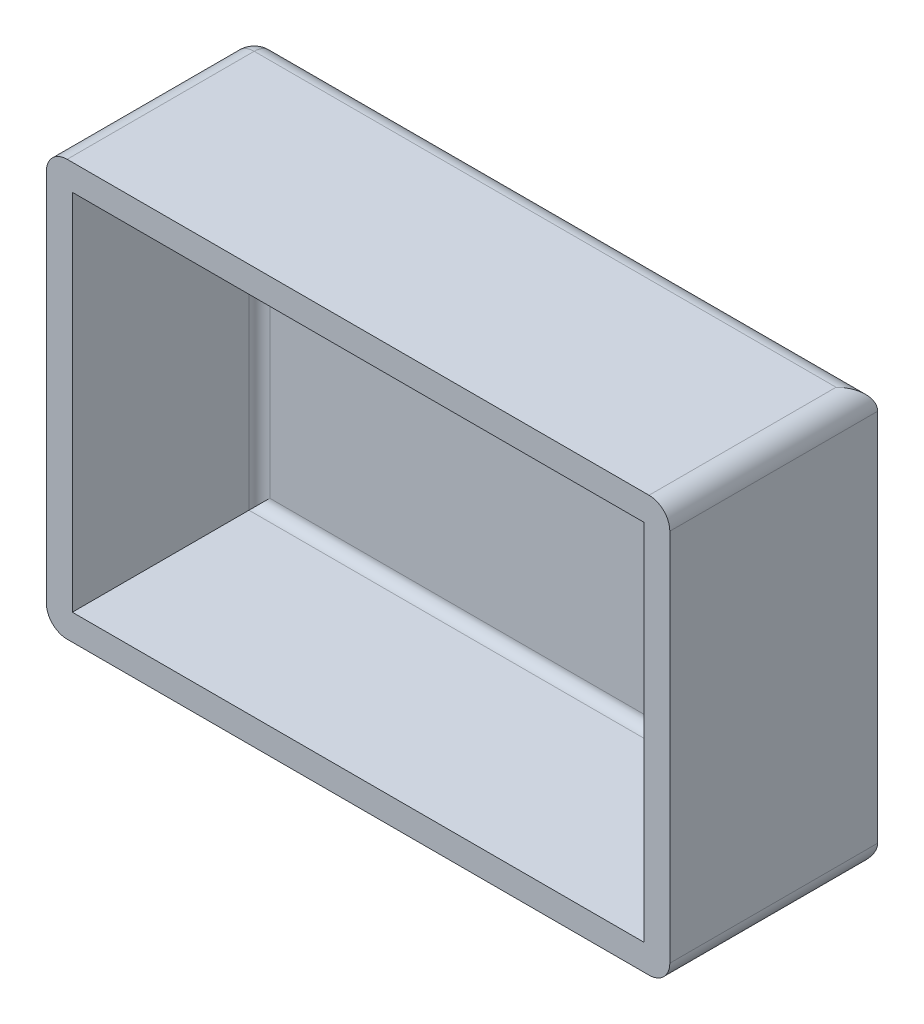
SolidWorks part; units mm, degrees
ref_plane "Front Plane" through (0, 0, 0) normal (0, 0, 1) x (1, 0, 0)
ref_plane "Top Plane" through (0, 0, 0) normal (0, 1, 0) x (1, 0, 0)
ref_plane "Right Plane" through (0, 0, 0) normal (1, 0, 0) x (0, 0, -1)
sketch "Sketch1" plane through (0, 0, 0) normal (0, 0, 1) x (1, 0, 0)
  line L1 (-30, -20) -> (30, -20)
  line L2 (-30, -20) -> (-30, 20)
  line L3 (-30, 20) -> (30, 20)
  line L4 (30, -20) -> (30, 20)
  line L5 (-30, -20) -> (30, 20) construction
  line L6 (-30, 20) -> (30, -20) construction
  point P0 (0, 0)
  dimension "D1" = 60
  dimension "D2" = 40
extrude "Boss-Extrude1" add sketch "Sketch1" along normal blind 20
sketch "Sketch2" plane through (0, 0, 20) normal (0, 0, 1) x (1, 0, 0)
  line L1 (-27.5, -17.5) -> (27.5, -17.5)
  line L2 (-27.5, -17.5) -> (-27.5, 17.5)
  line L3 (-27.5, 17.5) -> (27.5, 17.5)
  line L4 (27.5, -17.5) -> (27.5, 17.5)
  line L5 (-27.5, -17.5) -> (27.5, 17.5) construction
  line L6 (-27.5, 17.5) -> (27.5, -17.5) construction
  point P0 (0, 0)
  dimension "D1" = 55
  dimension "D2" = 35
extrude "Cut-Extrude1" cut sketch "Sketch2" against normal blind 18
fillet "Fillet1" radius 1 4 edges at (-27.5, 0, 2) (27.5, 0, 2) (0, -17.5, 2) (0, 17.5, 2)
fillet "Fillet2" radius 2 7 edges at (-30, -20, 10) (0, -20, 0) (30, -20, 10) (30, 20, 10) (0, 20, 0) (-30, 20, 10) (-30, 0, 0)
